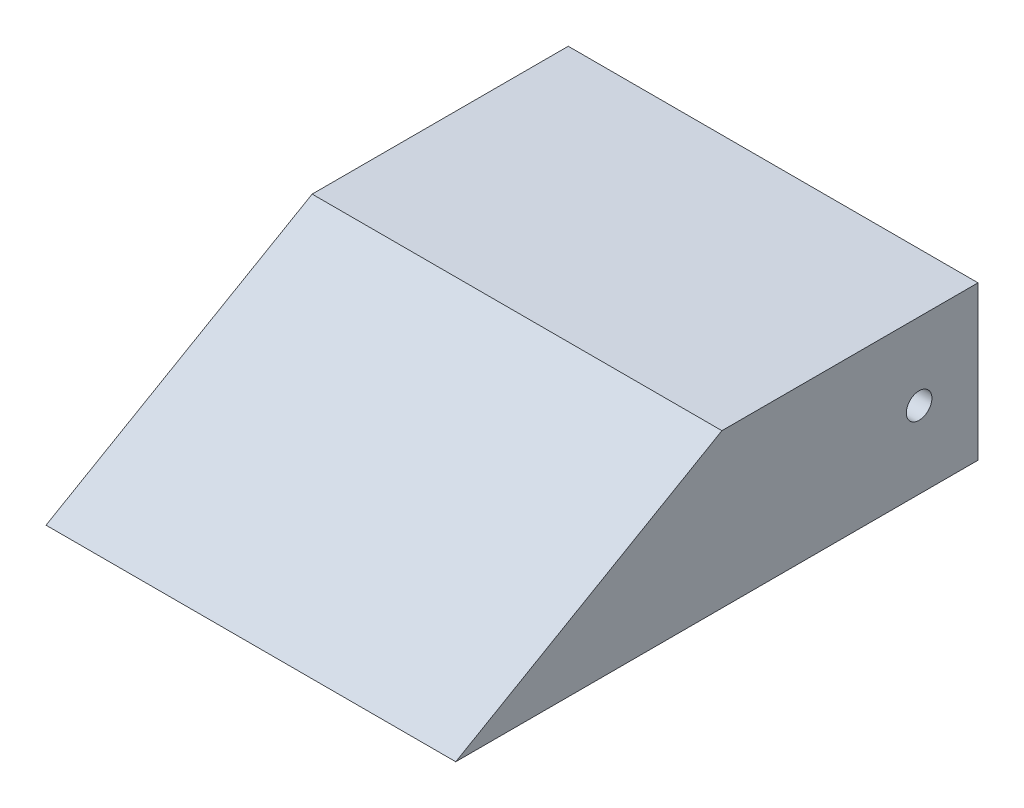
SolidWorks part; units mm, degrees
material "Nylon 101"
ref_plane "Front Plane" through (0, 0, 0) normal (0, 0, 1) x (1, 0, 0)
ref_plane "Top Plane" through (0, 0, 0) normal (0, 1, 0) x (1, 0, 0)
ref_plane "Right Plane" through (0, 0, 0) normal (1, 0, 0) x (0, 0, -1)
sketch "Sketch2" plane through (0, 0, 0) normal (0, 0, 1) x (1, 0, 0)
  line L1 (-80, -30) -> (80, -30)
  line L2 (-80, -30) -> (-80, 30)
  line L3 (-80, 30) -> (80, 30)
  line L4 (80, -30) -> (80, 30)
  line L5 (-80, -30) -> (80, 30) construction
  line L6 (-80, 30) -> (80, -30) construction
  point P0 (0, 0)
  dimension "D1" = 160
  dimension "D2" = 60
extrude "Boss-Extrude1" add sketch "Sketch2" along normal blind 230
sketch "Sketch3" plane through (80, 0, 0) normal (1, 0, 0) x (0, 0, -1)
  line L0 (-230, 30) -> (0, 30) construction
  line L1 (0, -30) -> (0, 30) construction
  line L2 (-100, 30) -> (-203.923, -30)
  line L3 (-230, -30) -> (0, -30) construction
  line L4 (-203.923, -30) -> (-230, -30)
  line L5 (-230, -30) -> (-230, 30)
  line L6 (-230, 30) -> (-100, 30)
  point P0 (-100, 30)
  dimension "D1" = 100
  dimension "D2" = 30
extrude "Cut-Extrude1" cut sketch "Sketch3" against normal up to next
shell "Shell1" thickness 10
sketch "Sketch5" plane through (80, 0, 0) normal (1, 0, 0) x (0, 0, -1)
  line L1 (0, -30) -> (0, 30) construction
  line L2 (-203.923, -30) -> (0, -30) construction
  circle A0 centre (-23, 0) radius 5
  dimension "D1" = 10
  dimension "D2" = 23
  dimension "D3" = 30
extrude "Cut-Extrude2" cut sketch "Sketch5" against normal through all
